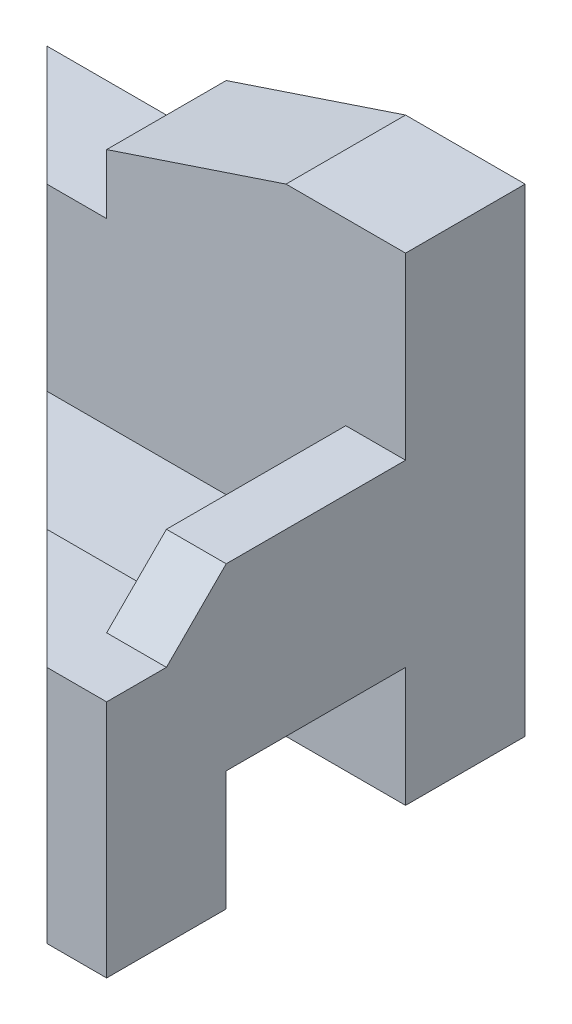
SolidWorks part; units mm, degrees
ref_plane "Front Plane" through (0, 0, 0) normal (0, 0, 1) x (1, 0, 0)
ref_plane "Top Plane" through (0, 0, 0) normal (0, 1, 0) x (1, 0, 0)
ref_plane "Right Plane" through (0, 0, 0) normal (1, 0, 0) x (0, 0, -1)
sketch "Sketch1" plane through (0, 0, 0) normal (0, 0, 1) x (1, 0, 0)
  line L1 (-20, 20) -> (20, 20)
  line L2 (-20, 20) -> (-20, -20)
  line L3 (-20, -20) -> (20, -20)
  line L4 (20, 20) -> (20, -20)
  line L5 (-20, 20) -> (20, -20) construction
  line L6 (-20, -20) -> (20, 20) construction
  point P0 (0, 0)
  dimension "D1" = 40
  dimension "D2" = 40
extrude "Boss-Extrude1" add sketch "Sketch1" along normal blind 10
sketch "Sketch2" plane through (0, 0, 10) normal (0, 0, 1) x (1, 0, 0)
  line L0 (10, 20) -> (-5, 15)
  line L1 (20, 20) -> (-20, 20) construction
  line L2 (-5, 15) -> (-5, 20)
  line L3 (-5, 20) -> (10, 20)
  dimension "D1" = 10
  dimension "D2" = 15
  dimension "D3" = 5
extrude "Cut-Extrude1" cut sketch "Sketch2" against normal through all
sketch "Sketch3" plane through (0, 0, 10) normal (0, 0, 1) x (1, 0, 0)
  line L0 (-5, 15) -> (-5, 10)
  line L1 (-5, 10) -> (-20, 10)
  line L2 (-20, 20) -> (-20, -20) construction
  line L3 (-20, 10) -> (-20, 20)
  line L4 (-20, 20) -> (-5, 20)
  line L5 (-5, 20) -> (-5, 15)
  dimension "D1" = 5
extrude "Cut-Extrude2" cut sketch "Sketch3" against normal through all
sketch "Sketch4" plane through (0, 0, 10) normal (0, 0, 1) x (1, 0, 0)
  line L0 (-20, 0) -> (20, 0)
  line L1 (-20, 10) -> (-20, -20) construction
  line L2 (20, -20) -> (20, 20) construction
  line L3 (20, 0) -> (20, -20)
  line L4 (20, -20) -> (-20, -20)
  line L5 (-20, -20) -> (-20, 0)
  dimension "D1" = 20
extrude "Boss-Extrude2" add sketch "Sketch4" along normal blind 25
sketch "Sketch5" plane through (-20, 0, 0) normal (-1, 0, 0) x (0, 0, 1)
  line L0 (10, 0) -> (10, -5)
  line L1 (10, -5) -> (25, -5)
  line L2 (25, -5) -> (25, 0)
  line L3 (35, 0) -> (10, 0) construction
  line L4 (25, 0) -> (10, 0)
  dimension "D1" = 10
  dimension "D2" = 5
extrude "Cut-Extrude3" cut sketch "Sketch5" against normal through all
sketch "Sketch7" plane through (-20, 0, 0) normal (-1, 0, 0) x (0, 0, 1)
  line L0 (10, -20) -> (10, -10)
  line L1 (35, -20) -> (0, -20) construction
  line L2 (10, -10) -> (25, -10)
  line L3 (25, -10) -> (25, -20)
  line L4 (25, -20) -> (10, -20)
  dimension "D1" = 10
  dimension "D2" = 10
  dimension "D3" = 10
extrude "Cut-Extrude4" cut sketch "Sketch7" against normal through all
sketch "Sketch8" plane through (0, 10, 0) normal (0, 1, 0) x (1, 0, 0)
  line L0 (-20, 0) -> (15, -35)
  line L1 (20, -35) -> (-20, -35) construction
  line L2 (15, -35) -> (-20, -35)
  line L3 (-20, -35) -> (-20, 0)
  dimension "D1" = 5
extrude "Cut-Extrude5" cut sketch "Sketch8" against normal through all
sketch "Sketch9" plane through (0, 0, 10) normal (0, 0, 1) x (1, 0, 0)
  line L0 (20, -5) -> (20, 5)
  line L1 (20, -5) -> (20, 20) construction
  line L2 (20, 5) -> (15, 5)
  line L3 (15, 5) -> (15, -5)
  line L4 (20, -5) -> (-10, -5) construction
  line L5 (15, -5) -> (20, -5)
  dimension "D1" = 5
  dimension "D2" = 10
extrude "Boss-Extrude3" add sketch "Sketch9" along normal blind 20
sketch "Sketch10" plane through (15, 0, 0) normal (-1, 0, 0) x (0, 0, 1)
  line L0 (30, 0) -> (25, 5)
  line L1 (30, 5) -> (10, 5) construction
  line L2 (25, 5) -> (30, 5)
  line L3 (30, 5) -> (30, 0)
  dimension "D1" = 5
extrude "Cut-Extrude6" cut sketch "Sketch10" against normal through all
